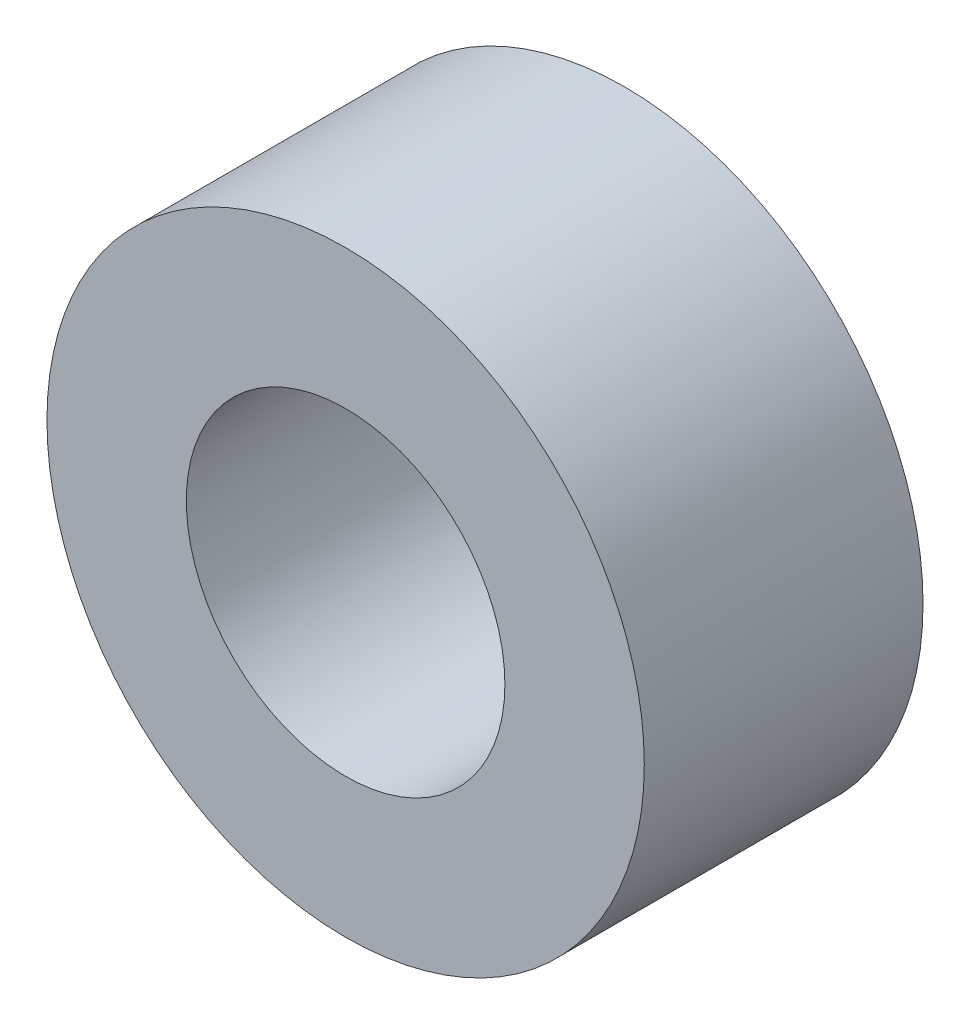
SolidWorks part; units mm, degrees
ref_plane "Front Plane" through (0, 0, 0) normal (0, 0, 1) x (1, 0, 0)
ref_plane "Top Plane" through (0, 0, 0) normal (0, 1, 0) x (1, 0, 0)
ref_plane "Right Plane" through (0, 0, 0) normal (1, 0, 0) x (0, 0, -1)
sketch "Sketch1" plane through (0, 0, 0) normal (0, 0, 1) x (1, 0, 0)
  circle A0 centre (0, 0) radius 7.5
  circle A1 centre (0, 0) radius 4
  dimension "D1" = 15
  dimension "D2" = 8
extrude "Boss-Extrude1" add sketch "Sketch1" along normal blind 7
